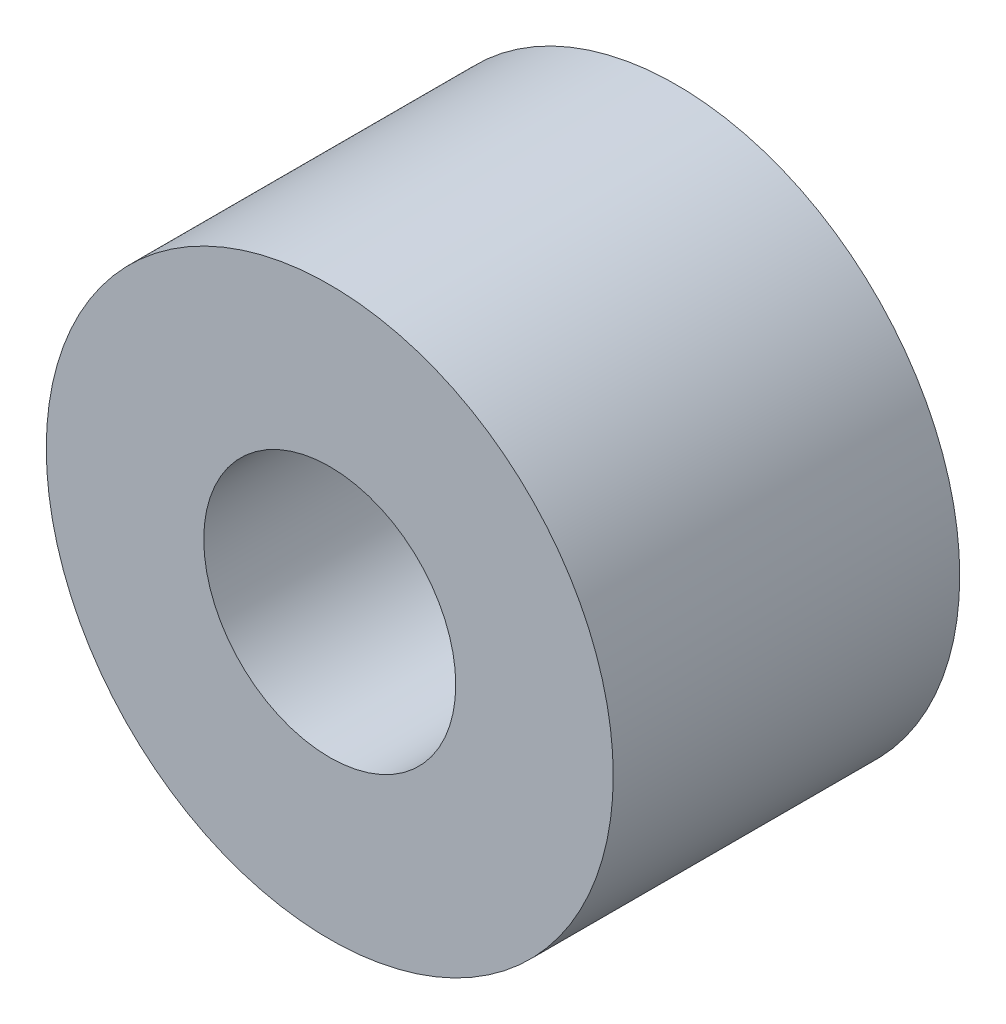
SolidWorks part; units mm, degrees
ref_plane "前视基准面" through (0, 0, 0) normal (0, 0, 1) x (1, 0, 0)
ref_plane "上视基准面" through (0, 0, 0) normal (0, 1, 0) x (1, 0, 0)
ref_plane "右视基准面" through (0, 0, 0) normal (1, 0, 0) x (0, 0, -1)
sketch "草图1" plane through (0, 0, 0) normal (0, 0, 1) x (1, 0, 0)
  circle A0 centre (0, 0) radius 2
  circle A1 centre (0, 0) radius 4.5
extrude "凸台-拉伸1" add sketch "草图1" along normal blind 5.5
